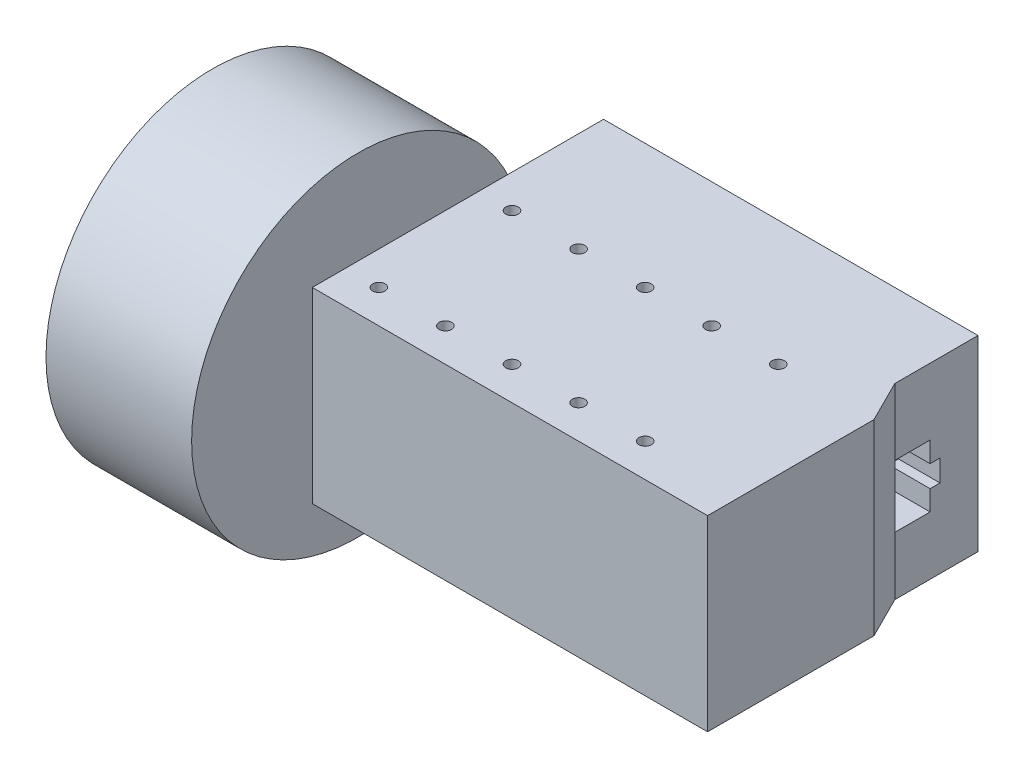
SolidWorks part; units mm, degrees
ref_plane "前视基准面" through (0, 0, 0) normal (0, 0, 1) x (1, 0, 0)
ref_plane "上视基准面" through (0, 0, 0) normal (0, 1, 0) x (1, 0, 0)
ref_plane "右视基准面" through (0, 0, 0) normal (1, 0, 0) x (0, 0, -1)
sketch "草图1" plane through (0, 0, 0) normal (0, 1, 0) x (1, 0, 0)
  line L0 (42.5, 35) -> (42.5, 15)
  line L1 (-47.5, 35) -> (42.5, 35)
  line L2 (-47.5, 35) -> (-47.5, -35)
  line L3 (-47.5, -35) -> (47.5, -35)
  line L4 (47.5, 5) -> (47.5, -35)
  line L5 (-47.5, 35) -> (47.5, -35) construction
  line L6 (-47.5, -35) -> (42.5, 31.3158) construction
  line L7 (42.5, 15) -> (47.5, 5)
  circle A0 centre (-39.5, -27) radius 1.5
  circle A1 centre (-23.5, -27) radius 1.5
  circle A2 centre (-7.5, -27) radius 1.5
  circle A3 centre (8.5, -27) radius 1.5
  circle A4 centre (24.5, -27) radius 1.5
  circle A5 centre (-23.5, 5) radius 1.5
  circle A6 centre (-7.5, 5) radius 1.5
  circle A7 centre (8.5, 5) radius 1.5
  circle A8 centre (24.5, 5) radius 1.5
  circle A9 centre (-39.5, 5) radius 1.5
  point P0 (0, 0)
  dimension "D6" = 3
  dimension "D1" = 95
  dimension "D2" = 70
  dimension "D3" = 20
  dimension "D4" = 10
  dimension "D5" = 90
  dimension "D7" = 8
  dimension "D8" = 8
  dimension "D9" = 5
  dimension "D10" = 2
extrude "凸台-拉伸1" add sketch "草图1" along normal blind 45
sketch "草图2" plane through (42.5, 0, 0) normal (1, 0, 0) x (0, 0, -1)
  line L0 (15, 45) -> (15, 0) construction
  line L1 (15, 29.0013) -> (23.4887, 29.0013)
  line L2 (15, 29.0013) -> (15, 14.0287)
  line L3 (15, 14.0287) -> (23.4887, 14.0287)
  line L4 (25.8667, 24.0691) -> (25.8667, 18.8727)
  line L8 (25.8667, 24.0691) -> (23.4887, 24.0691)
  line L9 (23.4887, 29.0013) -> (23.4887, 24.0691)
  line L12 (25.8667, 18.8727) -> (23.4887, 18.8727)
  line L13 (23.4887, 14.0287) -> (23.4887, 18.8727)
extrude "切除-拉伸1" cut sketch "草图2" against normal blind 10
sketch "草图3" plane through (-47.5, 0, 0) normal (-1, 0, 0) x (0, 0, 1)
  line L0 (35, 45) -> (35, 0) construction
  circle A0 centre (19, 22.5) radius 3
  point P4 (0, 0)
  point P5 (35, 22.5)
  point P6 (23.1256, 10.5796)
  dimension "D1" = 6
  dimension "D2" = 16
extrude "凸台-拉伸2" add sketch "草图3" along normal blind 5
sketch "草图4" plane through (-52.5, 0, 0) normal (-1, 0, 0) x (0, 0, 1)
  circle A0 centre (19, 22.5) radius 40
extrude "凸台-拉伸3" add sketch "草图4" along normal blind 35
